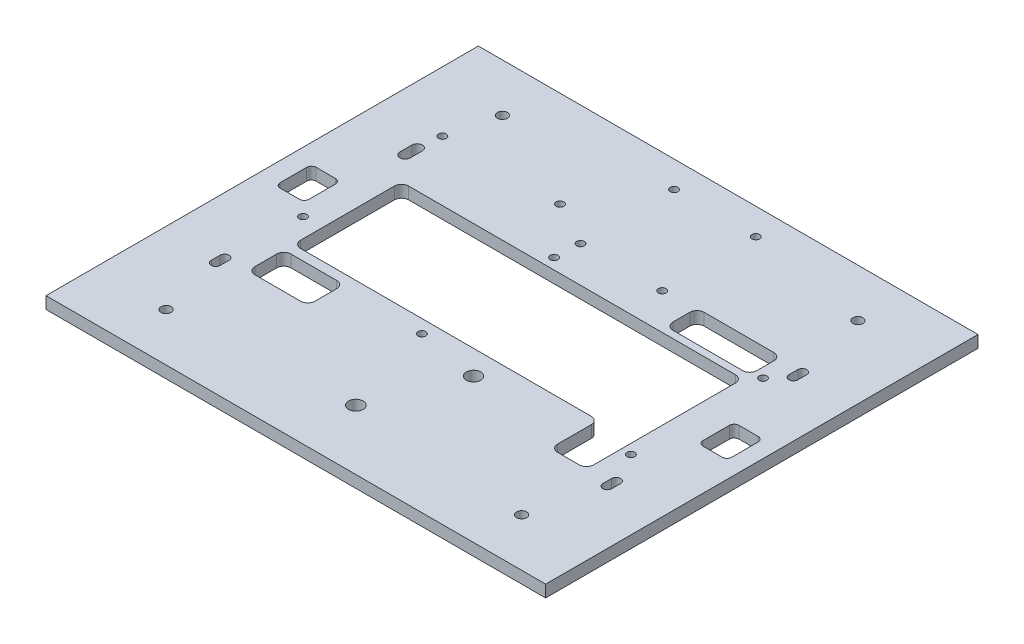
SolidWorks part; units mm, degrees
ref_plane "Front Plane" through (0, 0, 0) normal (0, 0, 1) x (1, 0, 0)
ref_plane "Top Plane" through (0, 0, 0) normal (0, 1, 0) x (1, 0, 0)
ref_plane "Right Plane" through (0, 0, 0) normal (1, 0, 0) x (0, 0, -1)
sketch "Dış Kesim" plane through (0, 0, 0) normal (0, 1, 0) x (1, 0, 0)
  line L1 (-104, -90) -> (104, -90)
  line L2 (-104, -90) -> (-104, 90)
  line L3 (-104, 90) -> (104, 90)
  line L4 (104, -90) -> (104, 90)
  dimension "D1" = 208
  dimension "D2" = 180
  dimension "D3" = 90
  dimension "D4" = 104
extrude "Ana Plaka" add sketch "Dış Kesim" along normal blind 5
sketch "BaseBoard + Pi" plane through (0, 0, 0) normal (0, 1, 0) x (1, 0, 0)
  line L0 (-104, 90) -> (-104, -90) construction
  line L1 (-79, 50) -> (-30, 50) construction
  line L2 (-79, 50) -> (-79, -8) construction
  line L3 (-79, -8) -> (-30, -8) construction
  line L4 (-30, 50) -> (-30, -8) construction
  circle A1 centre (-30, 50) radius 1.6
  circle A5 centre (-79, 50) radius 1.6
  circle A6 centre (-79, -8) radius 1.6
  dimension "D6" = 3.2
  dimension "D13" = 3.2
  dimension "D2" = 25
  dimension "D12" = 49
  dimension "D15" = 58
extrude "Base - Pi" cut sketch "BaseBoard + Pi" along normal through all
sketch "Robot Kasa Sınır" plane through (0, 0, 0) normal (0, 1, 0) x (1, 0, 0)
  line L1 (-84, -45) -> (84, -45) construction
  line L2 (-84, -45) -> (-84, 45) construction
  line L3 (-84, 45) -> (84, 45) construction
  line L4 (84, -45) -> (84, 45) construction
  dimension "D1" = 168
  dimension "D2" = 90
  dimension "D3" = 84
  dimension "D4" = 45
sketch "Sketch2" plane through (0, 5, 0) normal (0, 1, 0) x (1, 0, 0)
  line L0 (-84, -45) -> (-84, 45) construction
  line L1 (-84, 45) -> (84, 45) construction
  line L2 (-84, -45) -> (84, -45) construction
  line L3 (-80, 35.5) -> (-80, 40.5) construction
  line L4 (-82.15, 35.5) -> (-82.15, 40.5)
  line L5 (84, -45) -> (84, 45) construction
  line L6 (-77.85, 35.5) -> (-77.85, 40.5)
  line L7 (-80.5, -42.85) -> (-80.5, -39.15) construction
  line L8 (-82.35, -42.85) -> (-82.35, -39.15)
  line L9 (-78.65, -42.85) -> (-78.65, -39.15)
  line L10 (81.5, -41.85) -> (81.5, -38.15) construction
  line L11 (79.65, -41.85) -> (79.65, -38.15)
  line L12 (83.35, -41.85) -> (83.35, -38.15)
  line L13 (81, 36.15) -> (81, 39.85) construction
  line L14 (79.15, 36.15) -> (79.15, 39.85)
  line L15 (82.85, 36.15) -> (82.85, 39.85)
  arc A0 (-82.35, -42.85) -> (-78.65, -42.85) centre (-80.5, -42.85) ccw
  arc A1 (79.65, -41.85) -> (83.35, -41.85) centre (81.5, -41.85) ccw
  arc A2 (79.15, 36.15) -> (82.85, 36.15) centre (81, 36.15) ccw
  arc A3 (82.85, 39.85) -> (79.15, 39.85) centre (81, 39.85) ccw
  arc A4 (-82.15, 35.5) -> (-77.85, 35.5) centre (-80, 35.5) ccw
  arc A5 (-77.85, 40.5) -> (-82.15, 40.5) centre (-80, 40.5) ccw
  arc A6 (-78.65, -39.15) -> (-82.35, -39.15) centre (-80.5, -39.15) ccw
  arc A7 (83.35, -38.15) -> (79.65, -38.15) centre (81.5, -38.15) ccw
  point P14 (81, 38)
  point P18 (-80, 38)
  point P23 (-80.5, -41)
  point P31 (81.5, -40)
  dimension "D4" = 3.5
  dimension "D6" = 2.5
  dimension "D10" = 3
  dimension "D11" = 5
  dimension "D2" = 7
  dimension "D3" = 4
  dimension "D5" = 4
  dimension "D7" = 5
  dimension "D8" = 7
  dimension "D9" = 3.7
  dimension "D13" = 4.3
extrude "Kasa Bağlantıları" cut sketch "Sketch2" against normal through all
sketch "Sketch3" plane through (0, 5, 0) normal (0, 1, 0) x (1, 0, 0)
  line L0 (-59, 25) -> (-68, 25)
  line L1 (-68, -20) -> (53, -20)
  line L2 (-71, -17) -> (-71, 22)
  line L3 (-59, 25) -> (68, 25)
  line L4 (71, -15) -> (71, 22)
  line L6 (-68, -24) -> (-49, -24)
  line L7 (71, -15) -> (71, -37)
  line L8 (68, -40) -> (59, -40)
  line L9 (56, -23) -> (56, -37)
  line L10 (-71, -27) -> (-71, -36)
  line L12 (-68, -39) -> (-49, -39)
  line L21 (-46, -27) -> (-46, -36)
  arc A0 (-49, -24) -> (-46, -27) centre (-49, -27) cw
  arc A1 (-71, -36) -> (-68, -39) centre (-68, -36) ccw
  arc A2 (-49, -39) -> (-46, -36) centre (-49, -36) ccw
  arc A3 (-68, -24) -> (-71, -27) centre (-68, -27) ccw
  arc A4 (53, -20) -> (56, -23) centre (53, -23) cw
  arc A5 (71, -37) -> (68, -40) centre (68, -37) cw
  arc A6 (-71, 22) -> (-68, 25) centre (-68, 22) cw
  arc A7 (-68, -20) -> (-71, -17) centre (-68, -17) cw
  arc A8 (68, 25) -> (71, 22) centre (68, 22) cw
  arc A9 (59, -40) -> (56, -37) centre (59, -37) cw
  circle A10 centre (14, -30) radius 3
  point P13 (-46, -24)
  point P16 (-71, -39)
  point P19 (-46, -39)
  point P24 (56, -20)
  point P27 (71, -40)
  point P30 (-71, 25)
  point P33 (-71, -20)
  point P36 (71, 25)
  point P39 (56, -40)
  dimension "D9" = 4
  dimension "D10" = 6
  dimension "D12" = 3
  dimension "D1" = 142
  dimension "D2" = 45
  dimension "D3" = 20
  dimension "D4" = 15
  dimension "D5" = 25
  dimension "D6" = 71
  dimension "D7" = 0
  dimension "D8" = 25
  dimension "D11" = 15
extrude "LiPo Yuvası" cut sketch "Sketch3" against normal through all
sketch "Sketch1" plane through (0, 5, 0) normal (0, 1, 0) x (1, 0, 0)
  line L0 (104, 90) -> (-104, 90) construction
  line L1 (-12, 29.5) -> (75, 29.5) construction
  line L3 (-12, -25.5) -> (75, -25.5) construction
  line L4 (-12, -25.5) -> (-12, 29.5) construction
  line L5 (-12, 29.5) -> (75, 29.5) construction
  line L6 (75, -25.5) -> (75, 29.5) construction
  line L7 (-12, 29.5) -> (-12, -25.5) construction
  line L8 (-12, 2) -> (34.3441, 2) construction
  line L9 (104, -90) -> (104, 90) construction
  circle A0 centre (-12, 29.5) radius 1.6
  circle A1 centre (75, 29.5) radius 1.6
  circle A2 centre (75, -25.5) radius 1.6
  circle A3 centre (-12, -25.5) radius 1.6
  dimension "D3" = 3.2
  dimension "D6" = 3.2
  dimension "D1" = 88
  dimension "D2" = 29
  dimension "D4" = 87
  dimension "D5" = 55
extrude "MainBoard" cut sketch "Sketch1" against normal through all
sketch "Sketch5" plane through (0, 5, 0) normal (0, 1, 0) x (1, 0, 0)
  line L0 (104, -90) -> (104, 90) construction
  line L1 (-104, 90) -> (-104, -90) construction
  line L2 (104, 90) -> (-104, 90) construction
  line L4 (104, 70) -> (-104, 70) construction
  line L5 (0, 70) -> (0, 62.2161) construction
  line L6 (84, 0) -> (-84, 0) construction
  line L7 (84, -45) -> (84, 45) construction
  line L8 (-84, -45) -> (-84, 45) construction
  circle A0 centre (-74, 70) radius 2.1
  circle A1 centre (74, 70) radius 2.1
  circle A2 centre (74, -70) radius 2.1
  circle A3 centre (-74, -70) radius 2.1
  dimension "D1" = 4.2
  dimension "D3" = 30
  dimension "D2" = 20
extrude "Vida Delikleri" cut sketch "Sketch5" against normal through all
sketch "Sketch8" plane through (0, 5, 0) normal (0, 1, 0) x (1, 0, 0)
  line L1 (68, 25) -> (-68, 25) construction
  line L2 (68, 41) -> (39, 41)
  line L3 (71, 38) -> (71, 31)
  line L4 (68, 28) -> (39, 28)
  line L5 (36, 38) -> (36, 31)
  arc A0 (39, 41) -> (36, 38) centre (39, 38) ccw
  arc A1 (39, 28) -> (36, 31) centre (39, 31) cw
  arc A2 (68, 41) -> (71, 38) centre (68, 38) cw
  arc A3 (71, 31) -> (68, 28) centre (68, 31) cw
  point P6 (71, 22)
  point P9 (36, 41)
  point P15 (71, 41)
  point P18 (71, 28)
  dimension "D4" = 3
  dimension "D1" = 3
  dimension "D2" = 13
  dimension "D3" = 35
extrude "Kablo Aktarım Boşluğu" cut sketch "Sketch8" against normal through all
sketch "Sketch9" plane through (0, 5, 0) normal (0, 1, 0) x (1, 0, 0)
  line L1 (-94, 12.5) -> (-86, 12.5)
  line L2 (-96, 10.5) -> (-96, -0.5)
  line L3 (-94, -2.5) -> (-86, -2.5)
  line L4 (-84, 10.5) -> (-84, -0.5)
  line L5 (-104, 90) -> (-104, -90) construction
  line L6 (-84, 5) -> (-89.3952, 5) construction
  line L7 (95, 7.5) -> (87, 7.5)
  line L8 (97, 5.5) -> (97, -5.5)
  line L9 (95, -7.5) -> (87, -7.5)
  line L10 (85, 5.5) -> (85, -5.5)
  line L11 (104, 90) -> (-104, 90) construction
  line L12 (97, 0) -> (93.4198, 0) construction
  line L13 (104, -90) -> (104, 90) construction
  arc A0 (-86, 12.5) -> (-84, 10.5) centre (-86, 10.5) cw
  arc A1 (-96, -0.5) -> (-94, -2.5) centre (-94, -0.5) ccw
  arc A2 (-86, -2.5) -> (-84, -0.5) centre (-86, -0.5) ccw
  arc A3 (-94, 12.5) -> (-96, 10.5) centre (-94, 10.5) ccw
  arc A4 (87, 7.5) -> (85, 5.5) centre (87, 5.5) ccw
  arc A5 (97, -5.5) -> (95, -7.5) centre (95, -5.5) cw
  arc A6 (87, -7.5) -> (85, -5.5) centre (87, -5.5) cw
  arc A7 (95, 7.5) -> (97, 5.5) centre (95, 5.5) cw
  point P10 (-84, 12.5)
  point P15 (-84, -2.5)
  point P18 (-96, 12.5)
  point P31 (85, 7.5)
  point P34 (97, -7.5)
  point P39 (97, 7.5)
  dimension "D5" = 2
  dimension "D10" = 2
  dimension "D1" = 85
  dimension "D2" = 15
  dimension "D3" = 12
  dimension "D4" = 20
  dimension "D6" = 12
  dimension "D7" = 15
  dimension "D8" = 90
  dimension "D9" = 7
extrude "Sharp Sensor" cut sketch "Sketch9" against normal through all
sketch "Sketch10" plane through (0, 5, 0) normal (0, 1, 0) x (1, 0, 0)
  line L0 (104, 90) -> (-104, 90) construction
  line L3 (-104, 90) -> (-104, -90) construction
  line B0 (-11.5, 40) -> (-11.5, 79) construction
  line B1 (-11.5, 79) -> (22.5, 79) construction
  line B2 (22.5, 79) -> (22.5, 40) construction
  line B3 (22.5, 40) -> (-11.5, 40) construction
  line B4 (-11.5, 59.5) -> (-14.4019, 59.5) construction
  line B5 (-19, 37) -> (-19, 82) construction
  line B6 (-19, 37) -> (30, 37) construction
  line B7 (30, 37) -> (30, 82) construction
  line B8 (-19, 82) -> (30, 82) construction
  line B9 (5.5, 40) -> (5.5, 38.9432) construction
  line B10 (5.5, 37) -> (5.5, 38.9432) construction
  line B11 (-19, 59.5) -> (-14.4019, 59.5) construction
  circle B12 centre (-11.5, 40) radius 1.6
  circle B13 centre (22.5, 40) radius 1.6
  circle B14 centre (-11.5, 79) radius 1.6
  circle B15 centre (22.5, 79) radius 1.6
  dimension "D1" = 8
  dimension "D2" = 85
sketch_block_instance "Block7-1"
sketch_block "Block7" parameters "D1"=3.2, "D2"=3.2, "D4"=3.2, "D5"=3.2, "D3"=34, "D6"=39, "D7"=39, "D8"=34, "D9"=45, "D10"=49
sketch "Sketch11" plane through (0, 5, 0) normal (0, 1, 0) x (1, 0, 0)
  line L0 (0, -90) -> (0, -85.5199) construction
  line L1 (-104, -90) -> (104, -90) construction
  circle A0 centre (0, -65) radius 3.05
  dimension "D1" = 6.1
  dimension "D2" = 25
extrude "Stop Buton" cut sketch "Sketch11" against normal through all
extrude "Motor Driver" cut sketch "Sketch10" against normal through all
